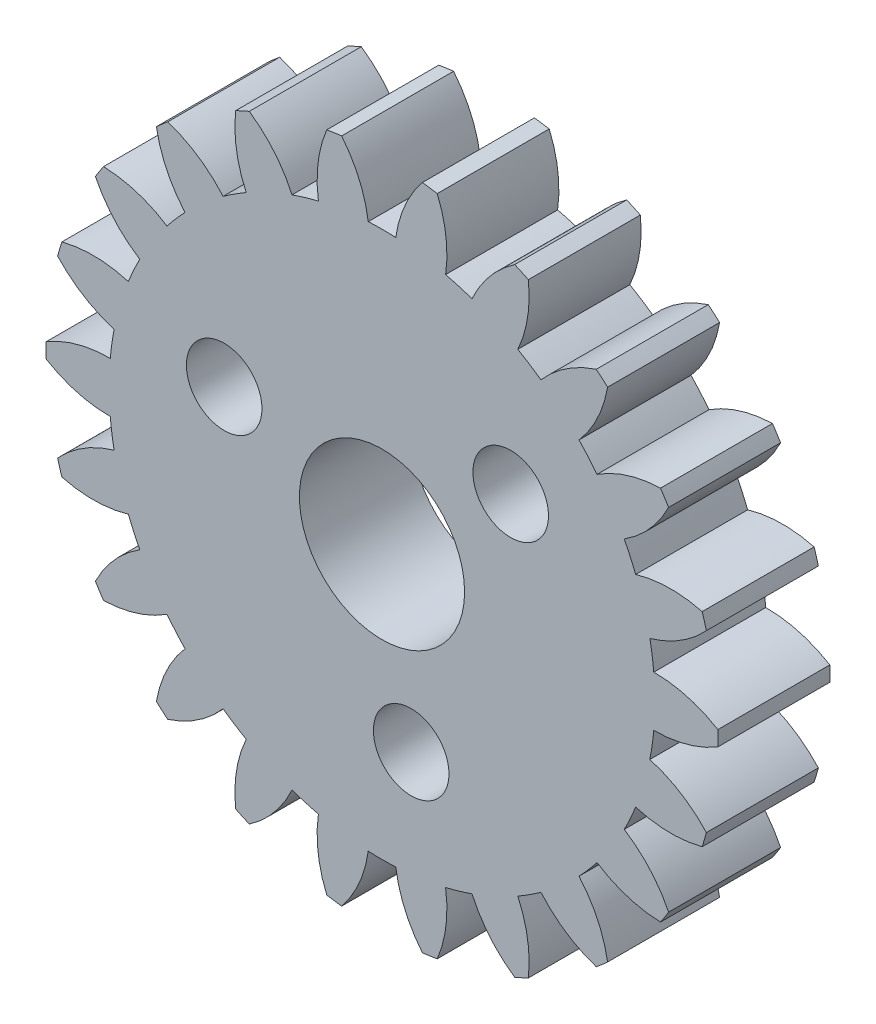
SolidWorks part; units mm, degrees
ref_plane "Front Plane" through (0, 0, 0) normal (0, 0, 1) x (1, 0, 0)
ref_plane "Top Plane" through (0, 0, 0) normal (0, 1, 0) x (1, 0, 0)
ref_plane "Right Plane" through (0, 0, 0) normal (1, 0, 0) x (0, 0, -1)
sketch "Model" plane through (0, 0, 0) normal (0, 0, 1) x (1, 0, 0)
  circle A0 centre (0, 0) radius 2.5
  arc A1 (-11.997, 0.2683) -> (-11.997, -0.2683) centre (0, 0) ccw
  arc A2 (-9.7074, 0.8997) -> (-11.997, 0.2683) centre (-9.7259, -3.5003) ccw
  arc A3 (-9.5676, 1.8717) -> (-9.7074, 0.8997) centre (0, 0) ccw
  arc A4 (-11.5866, 3.1225) -> (-9.5676, 1.8717) centre (-8.3458, 6.0986) ccw
  arc A5 (-11.4355, 3.6374) -> (-11.5866, 3.1225) centre (0, 0) ccw
  arc A6 (-9.0607, 3.5981) -> (-11.4355, 3.6374) centre (-10.3181, -0.6184) ccw
  arc A7 (-8.6528, 4.4914) -> (-9.0607, 3.5981) centre (0, 0) ccw
  arc A8 (-10.2376, 6.2604) -> (-8.6528, 4.4914) centre (-6.2896, 8.2029) ccw
  arc A9 (-9.9475, 6.7118) -> (-10.2376, 6.2604) centre (0, 0) ccw
  arc A10 (-7.68, 6.0051) -> (-9.9475, 6.7118) centre (-10.0744, 2.3136) ccw
  arc A11 (-7.0369, 6.7472) -> (-7.68, 6.0051) centre (0, 0) ccw
  arc A12 (-8.0591, 8.891) -> (-7.0369, 6.7472) centre (-3.7238, 9.6426) ccw
  arc A13 (-7.6536, 9.2424) -> (-8.0591, 8.891) centre (0, 0) ccw
  arc A14 (-5.6771, 7.9255) -> (-7.6536, 9.2424) centre (-9.0145, 5.0582) ccw
  arc A15 (-4.851, 8.4564) -> (-5.6771, 7.9255) centre (0, 0) ccw
  arc A16 (-5.2278, 10.8014) -> (-4.851, 8.4564) centre (-0.8563, 10.3011) ccw
  arc A17 (-4.7397, 11.0243) -> (-5.2278, 10.8014) centre (0, 0) ccw
  arc A18 (-3.2142, 9.2039) -> (-4.7397, 11.0243) centre (-7.2243, 7.3929) ccw
  arc A19 (-2.272, 9.4806) -> (-3.2142, 9.2039) centre (0, 0) ccw
  arc A20 (-1.9729, 11.8367) -> (-2.272, 9.4806) centre (2.0805, 10.1251) ccw
  arc A21 (-1.4418, 11.9131) -> (-1.9729, 11.8367) centre (0, 0) ccw
  arc A22 (-0.491, 9.7366) -> (-1.4418, 11.9131) centre (-4.8488, 9.1288) ccw
  arc A23 (0.491, 9.7366) -> (-0.491, 9.7366) centre (0, 0) ccw
  arc A24 (1.4418, 11.9131) -> (0.491, 9.7366) centre (4.8488, 9.1288) ccw
  arc A25 (1.9729, 11.8367) -> (1.4418, 11.9131) centre (0, 0) ccw
  arc A26 (2.272, 9.4806) -> (1.9729, 11.8367) centre (-2.0805, 10.1251) ccw
  arc A27 (3.2142, 9.2039) -> (2.272, 9.4806) centre (0, 0) ccw
  arc A28 (4.7397, 11.0243) -> (3.2142, 9.2039) centre (7.2243, 7.3929) ccw
  arc A29 (5.2278, 10.8014) -> (4.7397, 11.0243) centre (0, 0) ccw
  arc A30 (4.851, 8.4564) -> (5.2278, 10.8014) centre (0.8563, 10.3011) ccw
  arc A31 (5.6771, 7.9255) -> (4.851, 8.4564) centre (0, 0) ccw
  arc A32 (7.6536, 9.2424) -> (5.6771, 7.9255) centre (9.0145, 5.0582) ccw
  arc A33 (8.0591, 8.891) -> (7.6536, 9.2424) centre (0, 0) ccw
  arc A34 (7.0369, 6.7472) -> (8.0591, 8.891) centre (3.7238, 9.6426) ccw
  arc A35 (7.68, 6.0051) -> (7.0369, 6.7472) centre (0, 0) ccw
  arc A36 (9.9475, 6.7118) -> (7.68, 6.0051) centre (10.0744, 2.3136) ccw
  arc A37 (10.2376, 6.2604) -> (9.9475, 6.7118) centre (0, 0) ccw
  arc A38 (8.6528, 4.4914) -> (10.2376, 6.2604) centre (6.2896, 8.2029) ccw
  arc A39 (9.0607, 3.5981) -> (8.6528, 4.4914) centre (0, 0) ccw
  arc A40 (11.4355, 3.6374) -> (9.0607, 3.5981) centre (10.3181, -0.6184) ccw
  arc A41 (11.5866, 3.1225) -> (11.4355, 3.6374) centre (0, 0) ccw
  arc A42 (9.5676, 1.8717) -> (11.5866, 3.1225) centre (8.3458, 6.0986) ccw
  arc A43 (9.7074, 0.8997) -> (9.5676, 1.8717) centre (0, 0) ccw
  arc A44 (11.997, 0.2683) -> (9.7074, 0.8997) centre (9.7259, -3.5003) ccw
  arc A45 (11.997, -0.2683) -> (11.997, 0.2683) centre (0, 0) ccw
  arc A46 (9.7074, -0.8997) -> (11.997, -0.2683) centre (9.7259, 3.5003) ccw
  arc A47 (9.5676, -1.8717) -> (9.7074, -0.8997) centre (0, 0) ccw
  arc A48 (11.5866, -3.1225) -> (9.5676, -1.8717) centre (8.3458, -6.0986) ccw
  arc A49 (11.4355, -3.6374) -> (11.5866, -3.1225) centre (0, 0) ccw
  arc A50 (9.0607, -3.5981) -> (11.4355, -3.6374) centre (10.3181, 0.6184) ccw
  arc A51 (8.6528, -4.4914) -> (9.0607, -3.5981) centre (0, 0) ccw
  arc A52 (10.2376, -6.2604) -> (8.6528, -4.4914) centre (6.2896, -8.2029) ccw
  arc A53 (9.9475, -6.7118) -> (10.2376, -6.2604) centre (0, 0) ccw
  arc A54 (7.68, -6.0051) -> (9.9475, -6.7118) centre (10.0744, -2.3136) ccw
  arc A55 (7.0369, -6.7472) -> (7.68, -6.0051) centre (0, 0) ccw
  arc A56 (8.0591, -8.891) -> (7.0369, -6.7472) centre (3.7238, -9.6426) ccw
  arc A57 (7.6536, -9.2424) -> (8.0591, -8.891) centre (0, 0) ccw
  arc A58 (5.6771, -7.9255) -> (7.6536, -9.2424) centre (9.0145, -5.0582) ccw
  arc A59 (4.851, -8.4564) -> (5.6771, -7.9255) centre (0, 0) ccw
  arc A60 (5.2278, -10.8014) -> (4.851, -8.4564) centre (0.8563, -10.3011) ccw
  arc A61 (4.7397, -11.0243) -> (5.2278, -10.8014) centre (0, 0) ccw
  arc A62 (3.2142, -9.2039) -> (4.7397, -11.0243) centre (7.2243, -7.3929) ccw
  arc A63 (2.272, -9.4806) -> (3.2142, -9.2039) centre (0, 0) ccw
  arc A64 (1.9729, -11.8367) -> (2.272, -9.4806) centre (-2.0805, -10.1251) ccw
  arc A65 (1.4418, -11.9131) -> (1.9729, -11.8367) centre (0, 0) ccw
  arc A66 (0.491, -9.7366) -> (1.4418, -11.9131) centre (4.8488, -9.1288) ccw
  arc A67 (-0.491, -9.7366) -> (0.491, -9.7366) centre (0, 0) ccw
  arc A68 (-1.4418, -11.9131) -> (-0.491, -9.7366) centre (-4.8488, -9.1288) ccw
  arc A69 (-1.9729, -11.8367) -> (-1.4418, -11.9131) centre (0, 0) ccw
  arc A70 (-2.272, -9.4806) -> (-1.9729, -11.8367) centre (2.0805, -10.1251) ccw
  arc A71 (-3.2142, -9.2039) -> (-2.272, -9.4806) centre (0, 0) ccw
  arc A72 (-4.7397, -11.0243) -> (-3.2142, -9.2039) centre (-7.2243, -7.3929) ccw
  arc A73 (-5.2278, -10.8014) -> (-4.7397, -11.0243) centre (0, 0) ccw
  arc A74 (-4.851, -8.4564) -> (-5.2278, -10.8014) centre (-0.8563, -10.3011) ccw
  arc A75 (-5.6771, -7.9255) -> (-4.851, -8.4564) centre (0, 0) ccw
  arc A76 (-7.6536, -9.2424) -> (-5.6771, -7.9255) centre (-9.0145, -5.0582) ccw
  arc A77 (-8.0591, -8.891) -> (-7.6536, -9.2424) centre (0, 0) ccw
  arc A78 (-7.0369, -6.7472) -> (-8.0591, -8.891) centre (-3.7238, -9.6426) ccw
  arc A79 (-7.68, -6.0051) -> (-7.0369, -6.7472) centre (0, 0) ccw
  arc A80 (-9.9475, -6.7118) -> (-7.68, -6.0051) centre (-10.0744, -2.3136) ccw
  arc A81 (-10.2376, -6.2604) -> (-9.9475, -6.7118) centre (0, 0) ccw
  arc A82 (-8.6528, -4.4914) -> (-10.2376, -6.2604) centre (-6.2896, -8.2029) ccw
  arc A83 (-9.0607, -3.5981) -> (-8.6528, -4.4914) centre (0, 0) ccw
  arc A84 (-11.4355, -3.6374) -> (-9.0607, -3.5981) centre (-10.3181, 0.6184) ccw
  arc A85 (-11.5866, -3.1225) -> (-11.4355, -3.6374) centre (0, 0) ccw
  arc A86 (-9.5676, -1.8717) -> (-11.5866, -3.1225) centre (-8.3458, -6.0986) ccw
  arc A87 (-9.7074, -0.8997) -> (-9.5676, -1.8717) centre (0, 0) ccw
  arc A88 (-11.997, -0.2683) -> (-9.7074, -0.8997) centre (-9.7259, 3.5003) ccw
extrude "Boss-Extrude1" add sketch "Model" along normal blind 4
sketch "Sketch4" plane through (0, 0, 0) normal (0, 0, 1) x (1, 0, 0)
  circle A0 centre (0, 0) radius 11 construction
  dimension "D1" = 22
sketch "Sketch2" plane through (0, 0, 4) normal (0, 0, 1) x (1, 0, 0)
  circle A0 centre (0, 0) radius 2.95
  dimension "D1" = 5.9
extrude "Cut-Extrude1" cut sketch "Sketch2" against normal blind 4
sketch "Sketch3" plane through (0, 0, 4) normal (0, 0, 1) x (1, 0, 0)
  line L0 (0, 0) -> (-9.3925, 0) construction
  line L1 (0, 0) -> (-5.6382, 2.0521) construction
  circle A0 centre (-5.6382, 2.0521) radius 1.35
  dimension "D1" = 2.7
  dimension "D2" = 6
  dimension "D3" = 20
extrude "Cut-Extrude2" cut sketch "Sketch3" against normal blind 4
pattern_circular "CirPattern1" count 3 over 360 about axis through (0, 0, 0) along (0, 0, 1) of "Cut-Extrude2"
